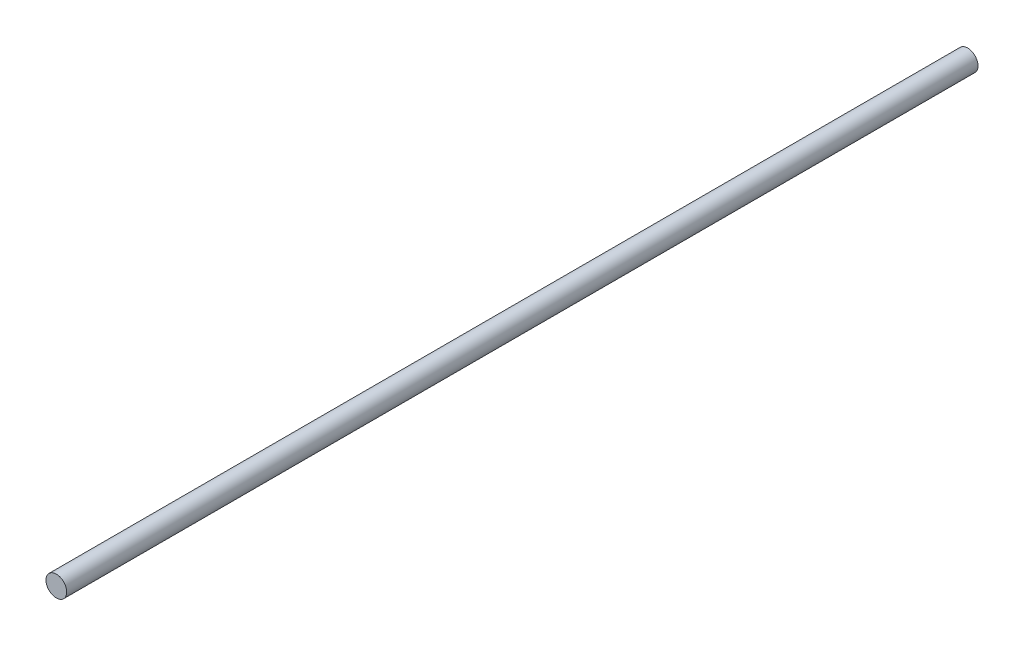
SolidWorks part; units mm, degrees
ref_plane "Front Plane" through (0, 0, 0) normal (0, 0, 1) x (1, 0, 0)
ref_plane "Top Plane" through (0, 0, 0) normal (0, 1, 0) x (1, 0, 0)
ref_plane "Right Plane" through (0, 0, 0) normal (1, 0, 0) x (0, 0, -1)
sketch "Sketch1" plane through (0, 0, 0) normal (0, 0, 1) x (1, 0, 0)
  circle A0 centre (0, 0) radius 3.175
  dimension "D1" = 6.35
extrude "Boss-Extrude1" add sketch "Sketch1" along normal blind 279.4
